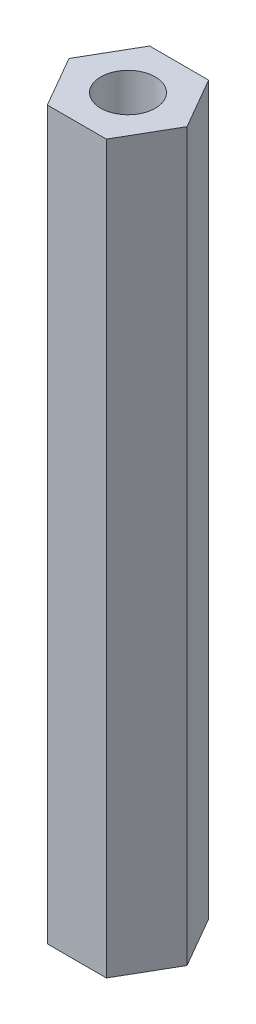
SolidWorks part; units mm, degrees
ref_plane "前视基准面" through (0, 0, 0) normal (0, 0, 1) x (1, 0, 0)
ref_plane "上视基准面" through (0, 0, 0) normal (0, 1, 0) x (1, 0, 0)
ref_plane "右视基准面" through (0, 0, 0) normal (1, 0, 0) x (0, 0, -1)
sketch "草图2" plane through (0, 0, 0) normal (0, 1, 0) x (1, 0, 0)
  line L1 (-1.625, 2.8146) -> (-3.25, 0)
  line L2 (-3.25, 0) -> (-1.625, -2.8146)
  line L3 (-1.625, -2.8146) -> (1.625, -2.8146)
  line L4 (1.625, -2.8146) -> (3.25, 0)
  line L5 (3.25, 0) -> (1.625, 2.8146)
  line L6 (1.625, 2.8146) -> (-1.625, 2.8146)
  circle A0 centre (0, 0) radius 3.25 construction
  circle A1 centre (0, 0) radius 1.5
  dimension "D1" = 3
  dimension "D2" = 6.5
extrude "凸台-拉伸1" add sketch "草图2" along normal blind 40
